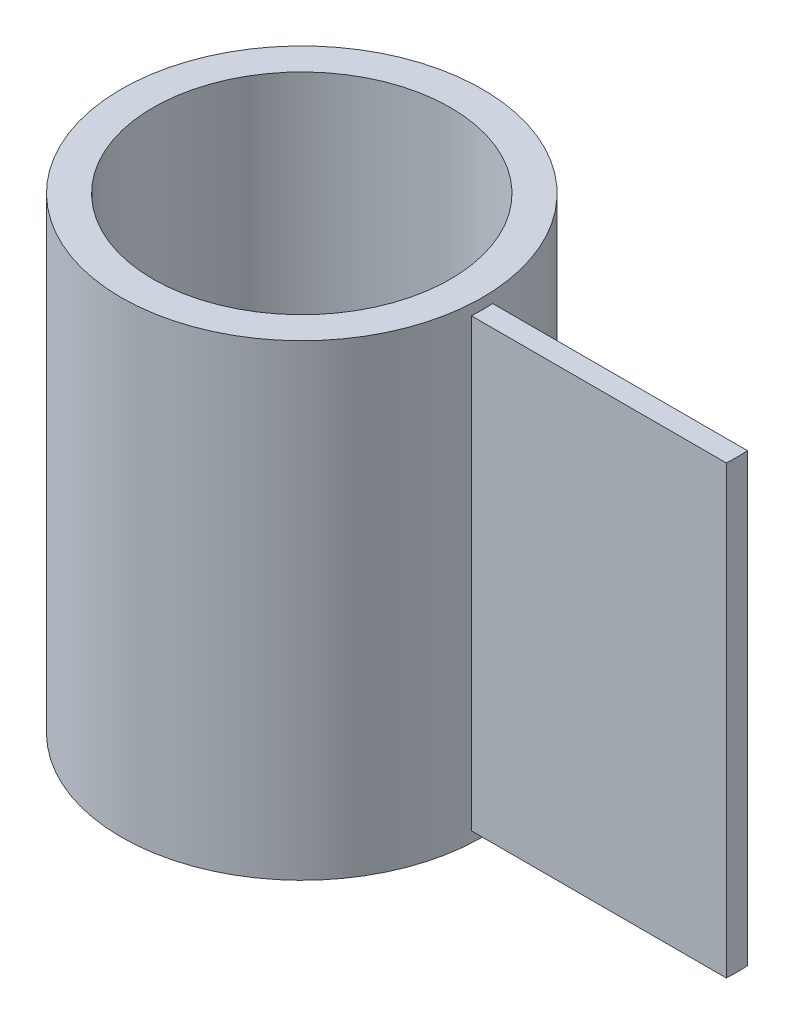
SolidWorks part; units mm, degrees
ref_plane "Front Plane" through (0, 0, 0) normal (0, 0, 1) x (1, 0, 0)
ref_plane "Top Plane" through (0, 0, 0) normal (0, 1, 0) x (1, 0, 0)
ref_plane "Right Plane" through (0, 0, 0) normal (1, 0, 0) x (0, 0, -1)
sketch "Sketch1" plane through (0, 0, 0) normal (0, 1, 0) x (1, 0, 0)
  circle A0 centre (0, 0) radius 35
  circle A1 centre (0, 0) radius 42.5
  dimension "D1" = 70
  dimension "D2" = 85
extrude "Boss-Extrude1" add sketch "Sketch1" along normal blind 110
sketch "Sketch2" plane through (0, 0, 0) normal (1, 0, 0) x (0, 0, -1)
  line L0 (0, 2.5) -> (0, 0) construction
  line L1 (2.5, 107.5) -> (-2.5, 107.5)
  line L2 (2.5, 107.5) -> (2.5, 2.5)
  line L3 (2.5, 2.5) -> (-2.5, 2.5)
  line L4 (-2.5, 107.5) -> (-2.5, 2.5)
  line L5 (2.5, 107.5) -> (-2.5, 2.5) construction
  line L6 (2.5, 2.5) -> (-2.5, 107.5) construction
  line L7 (0, 107.5) -> (0, 110) construction
  line L8 (35, 110) -> (-35, 110) construction
  point P0 (0, 55)
  dimension "D1" = 105
  dimension "D2" = 5
extrude "Boss-Extrude2" add sketch "Sketch2" along normal blind 60 from surface starting at face at (0, 110, 42.5)
